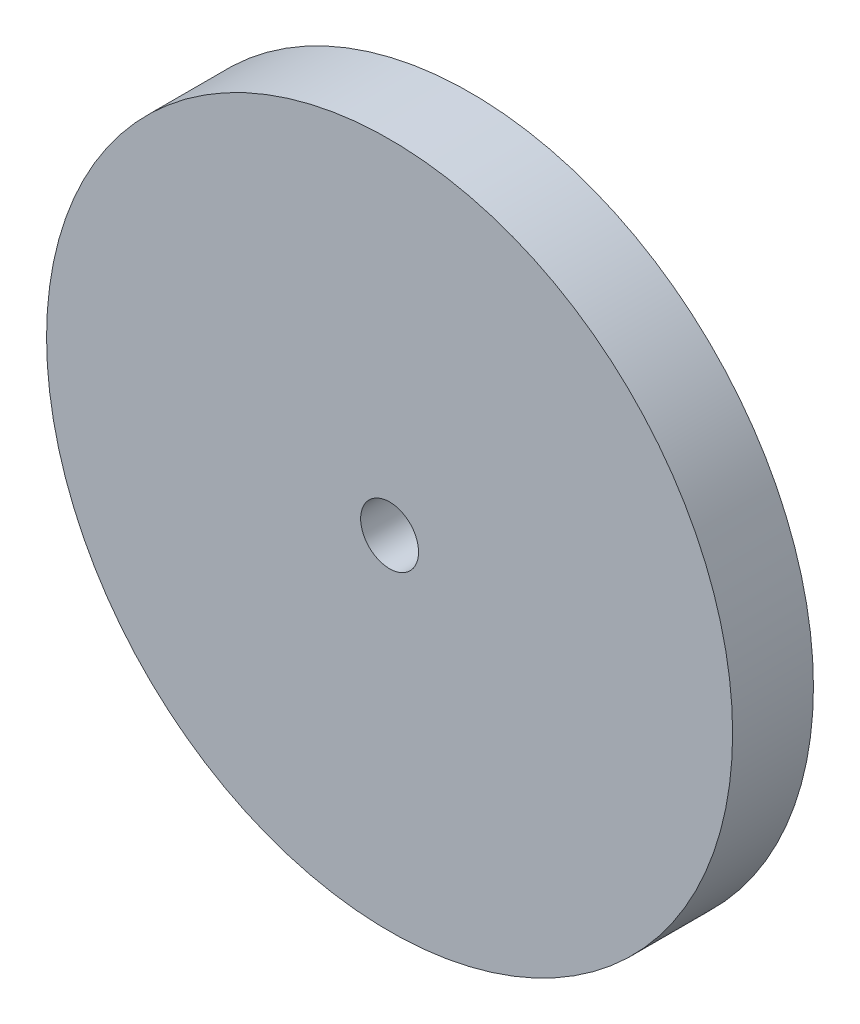
SolidWorks part; units mm, degrees
ref_plane "Front Plane" through (0, 0, 0) normal (0, 0, 1) x (1, 0, 0)
ref_plane "Top Plane" through (0, 0, 0) normal (0, 1, 0) x (1, 0, 0)
ref_plane "Right Plane" through (0, 0, 0) normal (1, 0, 0) x (0, 0, -1)
sketch "Sketch1" plane through (0, 0, 0) normal (0, 0, 1) x (1, 0, 0)
  circle A0 centre (0, 0) radius 32.3469
  dimension "D1" = 64.6938
extrude "Boss-Extrude1" add sketch "Sketch1" along normal mid plane 7.62
sketch "Sketch2" plane through (0, 0, 3.81) normal (0, 0, 1) x (1, 0, 0)
  circle A0 centre (0, 0) radius 2.7305
  dimension "D1" = 5.461
extrude "Cut-Extrude1" cut sketch "Sketch2" against normal up to surface (7.62 mm away) up to face at (32.3469, 0, -3.81)
